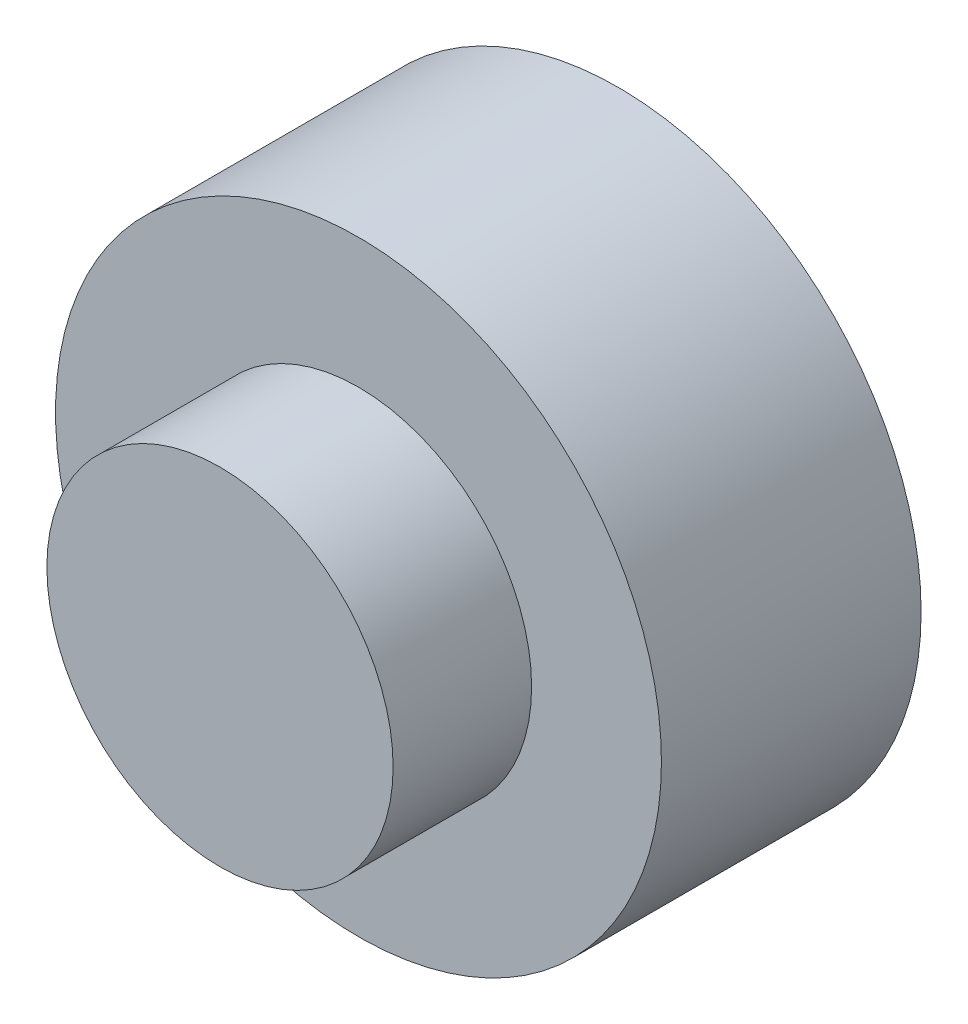
SolidWorks part; units mm, degrees
ref_plane "Front Plane" through (0, 0, 0) normal (0, 0, 1) x (1, 0, 0)
ref_plane "Top Plane" through (0, 0, 0) normal (0, 1, 0) x (1, 0, 0)
ref_plane "Right Plane" through (0, 0, 0) normal (1, 0, 0) x (0, 0, -1)
sketch "Sketch1" plane through (0, 0, 0) normal (0, 0, 1) x (1, 0, 0)
  circle A0 centre (0, 0) radius 17.5
  dimension "D1" = 35
extrude "Boss-Extrude1" add sketch "Sketch1" along normal blind 15
sketch "Sketch2" plane through (0, 0, 15) normal (0, 0, 1) x (1, 0, 0)
  circle A0 centre (0, 0) radius 10
  dimension "D1" = 20
extrude "Boss-Extrude2" add sketch "Sketch2" along normal blind 8
